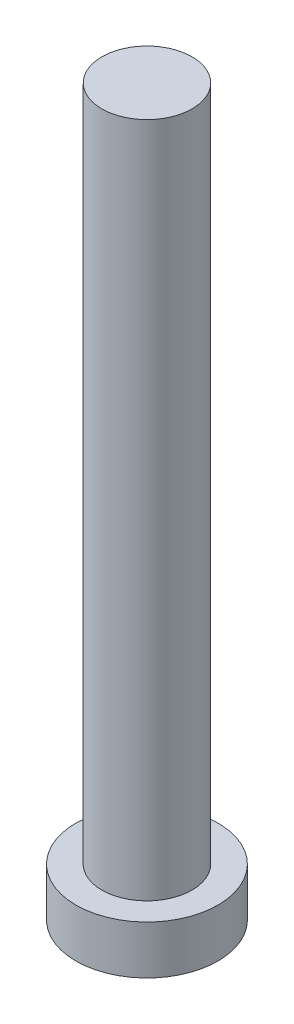
SolidWorks part; units mm, degrees
ref_plane "前视基准面" through (0, 0, 0) normal (0, 0, 1) x (1, 0, 0)
ref_plane "上视基准面" through (0, 0, 0) normal (0, 1, 0) x (1, 0, 0)
ref_plane "右视基准面" through (0, 0, 0) normal (1, 0, 0) x (0, 0, -1)
sketch "草图1" plane through (0, 0, 0) normal (0, 1, 0) x (1, 0, 0)
  circle A0 centre (0, 0) radius 3.15
extrude "凸台-拉伸1" add sketch "草图1" along normal blind 2.15
sketch "草图2" plane through (0, 2.15, 0) normal (0, 1, 0) x (1, 0, 0)
  circle A0 centre (0, 0) radius 2
extrude "凸台-拉伸2" add sketch "草图2" along normal blind 30
sketch "草图3" plane through (0, 0, 0) normal (0, -1, 0) x (1, 0, 0)
  line L0 (-0.5, 1) -> (-0.5, 2)
  line L1 (-2, -0.5) -> (-1, -0.5)
  line L2 (-2, -0.5) -> (-2, 0.5)
  line L3 (-2, 0.5) -> (-1, 0.5)
  line L4 (2, -0.5) -> (2, 0.5)
  line L5 (-2, -0.5) -> (2, 0.5) construction
  line L6 (-2, 0.5) -> (2, -0.5) construction
  line L7 (-0.5, -2) -> (0.5, -2)
  line L8 (-0.5, -2) -> (-0.5, -1)
  line L9 (-0.5, 2) -> (0.5, 2)
  line L10 (0.5, -2) -> (0.5, -1)
  line L11 (-0.5, -2) -> (0.5, 2) construction
  line L12 (-0.5, 2) -> (0.5, -2) construction
  line L13 (1, -0.5) -> (2, -0.5)
  line L14 (0.5, 1) -> (0.5, 2)
  line L15 (1, 0.5) -> (2, 0.5)
  arc A0 (-0.5, -1) -> (-1, -0.5) centre (-1, -1) ccw
  arc A1 (1, -0.5) -> (0.5, -1) centre (1, -1) ccw
  arc A2 (0.5, 1) -> (1, 0.5) centre (1, 1) ccw
  arc A3 (-0.5, 1) -> (-1, 0.5) centre (-1, 1) cw
  point P0 (0, 0)
  point P6 (0, 0)
  point P21 (0.5, 0.5)
  dimension "D1" = 0.5
extrude "切除-拉伸1" cut sketch "草图3" against normal blind 1.5
